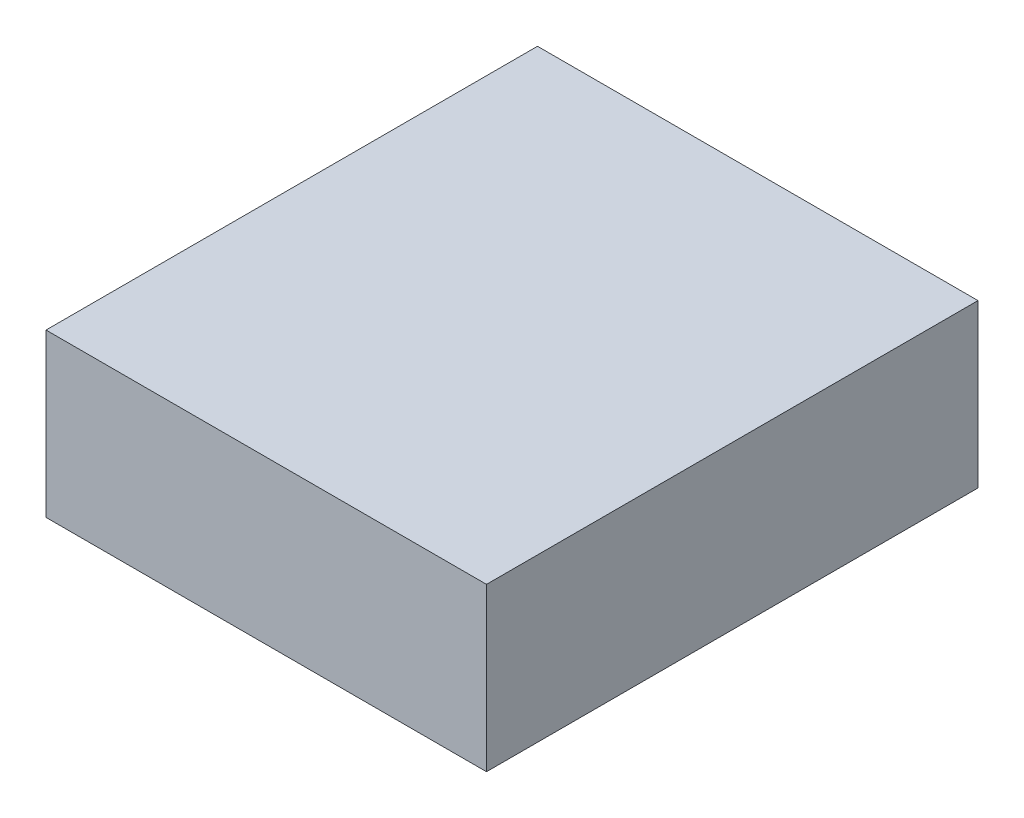
SolidWorks part; units mm, degrees
ref_plane "Front" through (0, 0, 0) normal (0, 0, 1) x (1, 0, 0)
ref_plane "Top" through (0, 0, 0) normal (0, 1, 0) x (1, 0, 0)
ref_plane "Right" through (0, 0, 0) normal (1, 0, 0) x (0, 0, -1)
sketch "Sketch1" plane through (0, 0, 0) normal (0, 1, 0) x (1, 0, 0)
  line L1 (-4.9677, 2.8646) -> (-1.1677, 2.8646)
  line L2 (-4.9677, 2.8646) -> (-4.9677, -1.3754)
  line L3 (-4.9677, -1.3754) -> (-1.1677, -1.3754)
  line L4 (-1.1677, 2.8646) -> (-1.1677, -1.3754)
  line L5 (-4.9677, 2.8646) -> (-1.1677, -1.3754) construction
  line L6 (-4.9677, -1.3754) -> (-1.1677, 2.8646) construction
  point P4 (-3.0677, 0.7446)
  dimension "D1" = 4.24
  dimension "D2" = 3.8
extrude "Boss-Extrude1" add sketch "Sketch1" along normal blind 1.4
